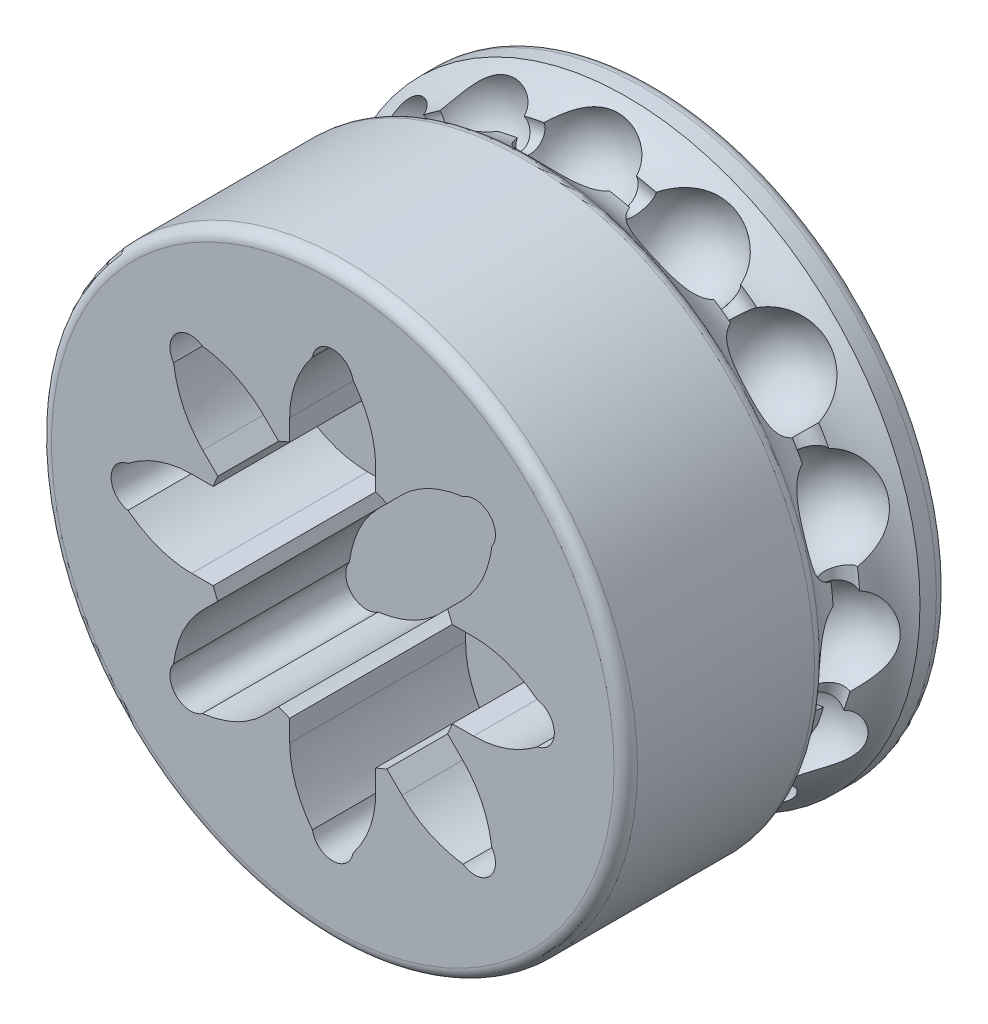
SolidWorks part; units mm, degrees
ref_plane "Plano frontal" through (0, 0, 0) normal (0, 0, 1) x (1, 0, 0)
ref_plane "Plano superior" through (0, 0, 0) normal (0, 1, 0) x (1, 0, 0)
ref_plane "Plano direito" through (0, 0, 0) normal (1, 0, 0) x (0, 0, -1)
sketch "Esboço1" plane through (0, 0, 0) normal (0, 0, 1) x (1, 0, 0)
  circle A0 centre (0, 0) radius 15
  dimension "D1" = 30
extrude "Ressalto-extrusão1" add sketch "Esboço1" along normal mid plane 8
sketch "Esboço2" plane through (0, 0, 0) normal (0, 0, 1) x (1, 0, 0)
  line L0 (0, 10.6681) -> (0, 15.6681)
  arc A1 (0, 15.6681) -> (0, 10.6681) centre (0, 13.1681) ccw
  dimension "D1" = 5
revolve "Corte-Revolução1" cut sketch "Esboço2" angle 360 about L0
pattern_circular "PadrãoCircular1" count 15 over 360 about axis through (0, 0, 0) along (0, 0, 1) of "Corte-Revolução1"
sketch "Esboço138" plane through (0, 0, 0) normal (0, 0, 1) x (1, 0, 0)
  circle A0 centre (0, 0) radius 17
  dimension "D1" = 34
sweep "Varredura de corte3" cut path "Esboço138" circular profile diameter 6.5 parameters "D3"=6.5
sketch "Esboço219" plane through (0, 0, 0) normal (0, 0, 1) x (1, 0, 0)
  circle A0 centre (0, 0) radius 13.5
  dimension "D1" = 27
sweep "Varredura de corte5" cut path "Esboço219" circular profile diameter 1.5 parameters "D3"=1.5
ref_plane "Plano1" through (0, 0, 12.5) normal (0, 0, 1) x (1, 0, 0)
sketch "Esboço244" plane through (0, 0, 12.5) normal (0, 0, 1) x (1, 0, 0)
  circle A1 centre (0, 0) radius 15
  dimension "D1" = 30
loft "Loft1" add profiles "Esboço244" section "Esboço244" section edge at (15, 0, 4)
sketch "Esboço248" plane through (0, 0, 12.5) normal (0, 0, 1) x (1, 0, 0)
  line L0 (-6.1164, 1.7) -> (-7.2123, 1.7)
  line L1 (-6.302, 3.8978) -> (-5.527, 3.1228)
  line L2 (-3.1228, 5.527) -> (-3.8978, 6.302)
  line L3 (-1.7, 7.2123) -> (-1.7, 6.1164)
  line L4 (1.7, 6.1164) -> (1.7, 7.2123)
  line L5 (3.8978, 6.302) -> (3.1228, 5.527)
  line L6 (5.527, 3.1228) -> (6.302, 3.8978)
  line L7 (7.2123, 1.7) -> (6.1164, 1.7)
  line L8 (6.1164, -1.7) -> (7.2123, -1.7)
  line L9 (6.302, -3.8978) -> (5.527, -3.1228)
  line L10 (3.1228, -5.527) -> (3.8978, -6.302)
  line L11 (1.7, -7.2123) -> (1.7, -6.1164)
  line L12 (-1.7, -6.1164) -> (-1.7, -7.2123)
  line L13 (-3.8978, -6.302) -> (-3.1228, -5.527)
  line L14 (-5.527, -3.1228) -> (-6.302, -3.8978)
  line L15 (-7.2123, -1.7) -> (-6.1164, -1.7)
  line L16 (-6.1164, 2.2) -> (-7.2123, 2.2)
  line L17 (-7.2123, -2.2) -> (-6.1164, -2.2)
  line L18 (-5.8806, -2.7693) -> (-6.6555, -3.5442)
  line L19 (-3.5442, -6.6555) -> (-2.7693, -5.8806)
  line L20 (-2.2, -6.1164) -> (-2.2, -7.2123)
  line L21 (2.2, -7.2123) -> (2.2, -6.1164)
  line L22 (2.7693, -5.8806) -> (3.5442, -6.6555)
  line L23 (6.6555, -3.5442) -> (5.8806, -2.7693)
  line L24 (6.1164, -2.2) -> (7.2123, -2.2)
  line L25 (7.2123, 2.2) -> (6.1164, 2.2)
  line L26 (5.8806, 2.7693) -> (6.6555, 3.5442)
  line L27 (3.5442, 6.6555) -> (2.7693, 5.8806)
  line L28 (2.2, 6.1164) -> (2.2, 7.2123)
  line L29 (-2.2, 7.2123) -> (-2.2, 6.1164)
  line L30 (-2.7693, 5.8806) -> (-3.5442, 6.6555)
  line L31 (-6.6555, 3.5442) -> (-5.8806, 2.7693)
  arc A0 (-5.4282, 2.5563) -> (-5.6459, 2.0308) centre (0, 0) ccw
  arc A1 (-6.1164, 1.7) -> (-5.6459, 2.0308) centre (-6.1164, 2.2) ccw
  arc A2 (-5.4282, 2.5563) -> (-5.527, 3.1228) centre (-5.8806, 2.7693) ccw
  arc A3 (-2.0308, 5.6459) -> (-2.5563, 5.4282) centre (0, 0) ccw
  arc A4 (-3.1228, 5.527) -> (-2.5563, 5.4282) centre (-2.7693, 5.8806) ccw
  arc A5 (-2.0308, 5.6459) -> (-1.7, 6.1164) centre (-2.2, 6.1164) ccw
  arc A6 (2.5563, 5.4282) -> (3.1228, 5.527) centre (2.7693, 5.8806) ccw
  arc A7 (2.5563, 5.4282) -> (2.0308, 5.6459) centre (0, 0) ccw
  arc A8 (1.7, 6.1164) -> (2.0308, 5.6459) centre (2.2, 6.1164) ccw
  arc A9 (5.6459, 2.0308) -> (6.1164, 1.7) centre (6.1164, 2.2) ccw
  arc A10 (5.6459, 2.0308) -> (5.4282, 2.5563) centre (0, 0) ccw
  arc A11 (5.527, 3.1228) -> (5.4282, 2.5563) centre (5.8806, 2.7693) ccw
  arc A12 (5.4282, -2.5563) -> (5.527, -3.1228) centre (5.8806, -2.7693) ccw
  arc A13 (5.4282, -2.5563) -> (5.6459, -2.0308) centre (0, 0) ccw
  arc A14 (6.1164, -1.7) -> (5.6459, -2.0308) centre (6.1164, -2.2) ccw
  arc A15 (2.0308, -5.6459) -> (1.7, -6.1164) centre (2.2, -6.1164) ccw
  arc A16 (2.0308, -5.6459) -> (2.5563, -5.4282) centre (0, 0) ccw
  arc A17 (3.1228, -5.527) -> (2.5563, -5.4282) centre (2.7693, -5.8806) ccw
  arc A18 (-2.5563, -5.4282) -> (-3.1228, -5.527) centre (-2.7693, -5.8806) ccw
  arc A19 (-2.5563, -5.4282) -> (-2.0308, -5.6459) centre (0, 0) ccw
  arc A20 (-1.7, -6.1164) -> (-2.0308, -5.6459) centre (-2.2, -6.1164) ccw
  arc A21 (-5.6459, -2.0308) -> (-6.1164, -1.7) centre (-6.1164, -2.2) ccw
  arc A22 (-5.6459, -2.0308) -> (-5.4282, -2.5563) centre (0, 0) ccw
  arc A23 (-5.527, -3.1228) -> (-5.4282, -2.5563) centre (-5.8806, -2.7693) ccw
  arc A24 (-7.6672, -6.8768) -> (-6.8768, -7.6672) centre (-7.272, -7.272) ccw
  arc A25 (-0.5589, -10.2842) -> (0.5589, -10.2842) centre (0, -10.2842) ccw
  arc A26 (6.8768, -7.6672) -> (7.6672, -6.8768) centre (7.272, -7.272) ccw
  arc A27 (10.2842, -0.5589) -> (10.2842, 0.5589) centre (10.2842, 0) ccw
  arc A28 (7.6672, 6.8768) -> (6.8768, 7.6672) centre (7.272, 7.272) ccw
  arc A29 (0.5589, 10.2842) -> (-0.5589, 10.2842) centre (0, 10.2842) ccw
  arc A30 (-6.8768, 7.6672) -> (-7.6672, 6.8768) centre (-7.272, 7.272) ccw
  arc A31 (-10.2842, 0.5589) -> (-10.2842, -0.5589) centre (-10.2842, 0) ccw
  arc A32 (-10.4792, 1.0408) -> (-10.4792, -1.0408) centre (-10.2842, 0) ccw
  arc A33 (-6.1164, -2.2) -> (-6.1164, -2.2) centre (-6.1164, -2.2) ccw
  arc A34 (-6.1164, -2.2) -> (-5.8806, -2.7693) centre (0, 0) ccw
  arc A35 (-5.8806, -2.7693) -> (-5.8806, -2.7693) centre (-5.8806, -2.7693) ccw
  arc A36 (-8.1459, -6.6739) -> (-6.6739, -8.1459) centre (-7.272, -7.272) ccw
  arc A37 (-2.7693, -5.8806) -> (-2.7693, -5.8806) centre (-2.7693, -5.8806) ccw
  arc A38 (-2.7693, -5.8806) -> (-2.2, -6.1164) centre (0, 0) ccw
  arc A39 (-2.2, -6.1164) -> (-2.2, -6.1164) centre (-2.2, -6.1164) ccw
  arc A40 (-1.0408, -10.4792) -> (1.0408, -10.4792) centre (0, -10.2842) ccw
  arc A41 (2.2, -6.1164) -> (2.2, -6.1164) centre (2.2, -6.1164) ccw
  arc A42 (2.2, -6.1164) -> (2.7693, -5.8806) centre (0, 0) ccw
  arc A43 (2.7693, -5.8806) -> (2.7693, -5.8806) centre (2.7693, -5.8806) ccw
  arc A44 (6.6739, -8.1459) -> (8.1459, -6.6739) centre (7.272, -7.272) ccw
  arc A45 (5.8806, -2.7693) -> (5.8806, -2.7693) centre (5.8806, -2.7693) ccw
  arc A46 (5.8806, -2.7693) -> (6.1164, -2.2) centre (0, 0) ccw
  arc A47 (6.1164, -2.2) -> (6.1164, -2.2) centre (6.1164, -2.2) ccw
  arc A48 (10.4792, -1.0408) -> (10.4792, 1.0408) centre (10.2842, 0) ccw
  arc A49 (6.1164, 2.2) -> (6.1164, 2.2) centre (6.1164, 2.2) ccw
  arc A50 (6.1164, 2.2) -> (5.8806, 2.7693) centre (0, 0) ccw
  arc A51 (5.8806, 2.7693) -> (5.8806, 2.7693) centre (5.8806, 2.7693) ccw
  arc A52 (8.1459, 6.6739) -> (6.6739, 8.1459) centre (7.272, 7.272) ccw
  arc A53 (2.7693, 5.8806) -> (2.7693, 5.8806) centre (2.7693, 5.8806) ccw
  arc A54 (2.7693, 5.8806) -> (2.2, 6.1164) centre (0, 0) ccw
  arc A55 (2.2, 6.1164) -> (2.2, 6.1164) centre (2.2, 6.1164) ccw
  arc A56 (1.0408, 10.4792) -> (-1.0408, 10.4792) centre (0, 10.2842) ccw
  arc A57 (-2.2, 6.1164) -> (-2.2, 6.1164) centre (-2.2, 6.1164) ccw
  arc A58 (-2.2, 6.1164) -> (-2.7693, 5.8806) centre (0, 0) ccw
  arc A59 (-2.7693, 5.8806) -> (-2.7693, 5.8806) centre (-2.7693, 5.8806) ccw
  arc A60 (-6.6739, 8.1459) -> (-8.1459, 6.6739) centre (-7.272, 7.272) ccw
  arc A61 (-5.8806, 2.7693) -> (-5.8806, 2.7693) centre (-5.8806, 2.7693) ccw
  arc A62 (-5.8806, 2.7693) -> (-6.1164, 2.2) centre (0, 0) ccw
  arc A63 (-6.1164, 2.2) -> (-6.1164, 2.2) centre (-6.1164, 2.2) ccw
  spline S0 degree 2 poles (-0.5589, 10.2842) (-1.7, 8.8508) (-1.7, 7.2123) knots 0 0 0 1 1 1
  spline S1 degree 2 poles (0.5589, 10.2842) (1.7, 8.8508) (1.7, 7.2123) knots 0 0 0 1 1 1
  spline S2 degree 2 poles (3.8978, 6.302) (5.0564, 7.4606) (6.8768, 7.6672) knots 0 0 0 1 1 1
  spline S3 degree 2 poles (7.6672, 6.8768) (7.4606, 5.0564) (6.302, 3.8978) knots 0 0 0 1 1 1
  spline S4 degree 2 poles (7.2123, 1.7) (8.8508, 1.7) (10.2842, 0.5589) knots 0 0 0 1 1 1
  spline S5 degree 2 poles (10.2842, -0.5589) (8.8508, -1.7) (7.2123, -1.7) knots 0 0 0 1 1 1
  spline S6 degree 2 poles (6.302, -3.8978) (7.4606, -5.0564) (7.6672, -6.8768) knots 0 0 0 1 1 1
  spline S7 degree 2 poles (3.8978, -6.302) (5.0564, -7.4606) (6.8768, -7.6672) knots 0 0 0 1 1 1
  spline S8 degree 2 poles (1.7, -7.2123) (1.7, -8.8508) (0.5589, -10.2842) knots 0 0 0 1 1 1
  spline S9 degree 2 poles (-1.7, -7.2123) (-1.7, -8.8508) (-0.5589, -10.2842) knots 0 0 0 1 1 1
  spline S10 degree 2 poles (-3.8978, -6.302) (-5.0564, -7.4606) (-6.8768, -7.6672) knots 0 0 0 1 1 1
  spline S11 degree 2 poles (-6.302, -3.8978) (-7.4606, -5.0564) (-7.6672, -6.8768) knots 0 0 0 1 1 1
  spline S12 degree 2 poles (-7.2123, -1.7) (-8.8508, -1.7) (-10.2842, -0.5589) knots 0 0 0 1 1 1
  spline S13 degree 2 poles (-7.2123, 1.7) (-8.8508, 1.7) (-10.2842, 0.5589) knots 0 0 0 1 1 1
  spline S14 degree 2 poles (-6.302, 3.8978) (-7.4606, 5.0564) (-7.6672, 6.8768) knots 0 0 0 1 1 1
  spline S15 degree 2 poles (-3.8978, 6.302) (-5.0564, 7.4606) (-6.8768, 7.6672) knots 0 0 0 1 1 1
  spline S16 degree 1 poles (-7.2123, 2.2) (-10.4792, 1.0408) knots 0 0 1 1 construction
  spline S17 degree 1 poles (-7.2123, -2.2) (-10.4792, -1.0408) knots 0 0 1 1 construction
  spline S18 degree 1 poles (-6.6555, -3.5442) (-8.1459, -6.6739) knots 0 0 1 1 construction
  spline S19 degree 1 poles (-3.5442, -6.6555) (-6.6739, -8.1459) knots 0 0 1 1 construction
  spline S20 degree 1 poles (-2.2, -7.2123) (-1.0408, -10.4792) knots 0 0 1 1 construction
  spline S21 degree 1 poles (2.2, -7.2123) (1.0408, -10.4792) knots 0 0 1 1 construction
  spline S22 degree 1 poles (3.5442, -6.6555) (6.6739, -8.1459) knots 0 0 1 1 construction
  spline S23 degree 1 poles (6.6555, -3.5442) (8.1459, -6.6739) knots 0 0 1 1 construction
  spline S24 degree 1 poles (10.4792, -1.0408) (7.2123, -2.2) knots 0 0 1 1 construction
  spline S25 degree 1 poles (7.2123, 2.2) (10.4792, 1.0408) knots 0 0 1 1 construction
  spline S26 degree 1 poles (8.1459, 6.6739) (6.6555, 3.5442) knots 0 0 1 1 construction
  spline S27 degree 1 poles (3.5442, 6.6555) (6.6739, 8.1459) knots 0 0 1 1 construction
  spline S28 degree 1 poles (1.0408, 10.4792) (2.2, 7.2123) knots 0 0 1 1 construction
  spline S29 degree 1 poles (-1.0408, 10.4792) (-2.2, 7.2123) knots 0 0 1 1 construction
  spline S30 degree 1 poles (-3.5442, 6.6555) (-6.6739, 8.1459) knots 0 0 1 1 construction
  spline S31 degree 1 poles (-6.6555, 3.5442) (-8.1459, 6.6739) knots 0 0 1 1 construction
  spline S32 degree 3 poles (-7.2123, 2.2) (-7.7865, 2.2) (-8.6507, 2.0511) (-9.7156, 1.5684) (-10.2362, 1.226) (-10.4792, 1.0408) knots 0 0 0 0 0.481198 0.721797 0.962395 0.962395 0.962395 0.962395
  spline S33 degree 3 poles (-10.4792, -1.0408) (-10.2362, -1.226) (-9.7156, -1.5684) (-8.6507, -2.0511) (-7.7865, -2.2) (-7.2123, -2.2) knots 0 0 0 0 0.240599 0.481198 0.962395 0.962395 0.962395 0.962395
  spline S34 degree 3 poles (-6.6555, -3.5442) (-7.0615, -3.9502) (-7.5673, -4.6667) (-7.979, -5.7609) (-8.105, -6.3712) (-8.1459, -6.6739) knots 0 0 0 0 0.481198 0.721797 0.962395 0.962395 0.962395 0.962395
  spline S35 degree 3 poles (-6.6739, -8.1459) (-6.3712, -8.105) (-5.7609, -7.979) (-4.6667, -7.5673) (-3.9502, -7.0615) (-3.5442, -6.6555) knots 0 0 0 0 0.240599 0.481198 0.962395 0.962395 0.962395 0.962395
  spline S36 degree 3 poles (-2.2, -7.2123) (-2.2, -7.7865) (-2.0511, -8.6507) (-1.5684, -9.7156) (-1.226, -10.2362) (-1.0408, -10.4792) knots 0 0 0 0 0.481198 0.721797 0.962395 0.962395 0.962395 0.962395
  spline S37 degree 3 poles (1.0408, -10.4792) (1.226, -10.2362) (1.5684, -9.7156) (2.0511, -8.6507) (2.2, -7.7865) (2.2, -7.2123) knots 0 0 0 0 0.240599 0.481198 0.962395 0.962395 0.962395 0.962395
  spline S38 degree 3 poles (3.5442, -6.6555) (3.9502, -7.0615) (4.6667, -7.5673) (5.7609, -7.979) (6.3712, -8.105) (6.6739, -8.1459) knots 0 0 0 0 0.481198 0.721797 0.962395 0.962395 0.962395 0.962395
  spline S39 degree 3 poles (8.1459, -6.6739) (8.105, -6.3712) (7.979, -5.7609) (7.5673, -4.6667) (7.0615, -3.9502) (6.6555, -3.5442) knots 0 0 0 0 0.240599 0.481198 0.962395 0.962395 0.962395 0.962395
  spline S40 degree 3 poles (7.2123, -2.2) (7.7865, -2.2) (8.6507, -2.0511) (9.7156, -1.5684) (10.2362, -1.226) (10.4792, -1.0408) knots 0.037605 0.037605 0.037605 0.037605 0.518802 0.759401 1 1 1 1
  spline S41 degree 3 poles (10.4792, 1.0408) (10.2362, 1.226) (9.7156, 1.5684) (8.6507, 2.0511) (7.7865, 2.2) (7.2123, 2.2) knots 0 0 0 0 0.240599 0.481198 0.962395 0.962395 0.962395 0.962395
  spline S42 degree 3 poles (6.6555, 3.5442) (7.0615, 3.9502) (7.5673, 4.6667) (7.979, 5.7609) (8.105, 6.3712) (8.1459, 6.6739) knots 0.037605 0.037605 0.037605 0.037605 0.518802 0.759401 1 1 1 1
  spline S43 degree 3 poles (6.6739, 8.1459) (6.3712, 8.105) (5.7609, 7.979) (4.6667, 7.5673) (3.9502, 7.0615) (3.5442, 6.6555) knots 0 0 0 0 0.240599 0.481198 0.962395 0.962395 0.962395 0.962395
  spline S44 degree 3 poles (2.2, 7.2123) (2.2, 7.7865) (2.0511, 8.6507) (1.5684, 9.7156) (1.226, 10.2362) (1.0408, 10.4792) knots 0.037605 0.037605 0.037605 0.037605 0.518802 0.759401 1 1 1 1
  spline S45 degree 3 poles (-1.0408, 10.4792) (-1.226, 10.2362) (-1.5684, 9.7156) (-2.0511, 8.6507) (-2.2, 7.7865) (-2.2, 7.2123) knots 0.037605 0.037605 0.037605 0.037605 0.278203 0.518802 1 1 1 1
  spline S46 degree 3 poles (-3.5442, 6.6555) (-3.9502, 7.0615) (-4.6667, 7.5673) (-5.7609, 7.979) (-6.3712, 8.105) (-6.6739, 8.1459) knots 0 0 0 0 0.481198 0.721797 0.962395 0.962395 0.962395 0.962395
  spline S47 degree 3 poles (-8.1459, 6.6739) (-8.105, 6.3712) (-7.979, 5.7609) (-7.5673, 4.6667) (-7.0615, 3.9502) (-6.6555, 3.5442) knots 0 0 0 0 0.240599 0.481198 0.962395 0.962395 0.962395 0.962395
  dimension "D1" = 0.5
extrude "Corte-extrusão1" cut sketch "Esboço248" against normal blind 9
fillet "Filete1" radius 0.6 3 edges at (15, 0, 12.5) (15, 0, -4) (-15, 0, 2.5617)
